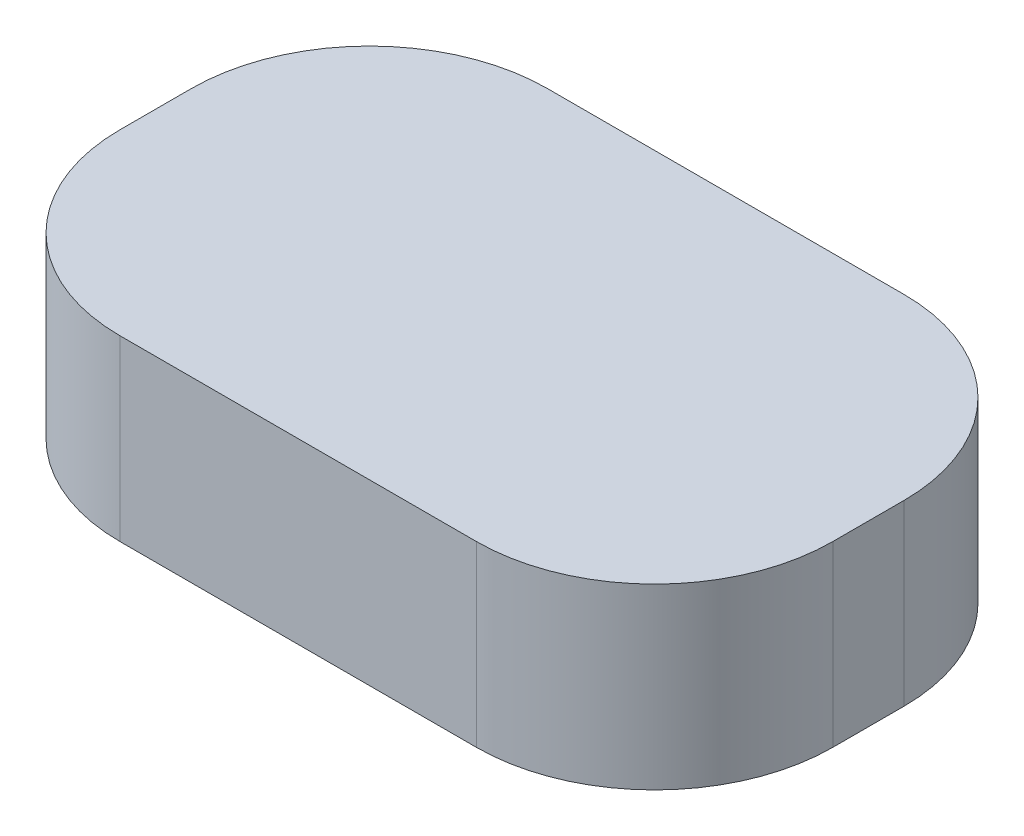
SolidWorks part; units mm, degrees
ref_plane "Front Plane" through (0, 0, 0) normal (0, 0, 1) x (1, 0, 0)
ref_plane "Top Plane" through (0, 0, 0) normal (0, 1, 0) x (1, 0, 0)
ref_plane "Right Plane" through (0, 0, 0) normal (1, 0, 0) x (0, 0, -1)
sketch "Sketch1" plane through (0, 0, 0) normal (0, 1, 0) x (1, 0, 0)
  line L1 (5, 0) -> (15, 0)
  line L2 (0, -5) -> (0, -7)
  line L3 (5, -12) -> (15, -12)
  line L4 (20, -5) -> (20, -7)
  arc A0 (15, -12) -> (20, -7) centre (15, -7) ccw
  arc A1 (20, -5) -> (15, 0) centre (15, -5) ccw
  arc A2 (0, -5) -> (5, 0) centre (5, -5) cw
  arc A3 (5, -12) -> (0, -7) centre (5, -7) cw
  point P11 (0, 0)
  dimension "D1" = 5
  dimension "D2" = 5
  dimension "D3" = 5
  dimension "D4" = 5
  dimension "D5" = 20
  dimension "D6" = 12
extrude "Boss-Extrude1" add sketch "Sketch1" along normal blind 5
